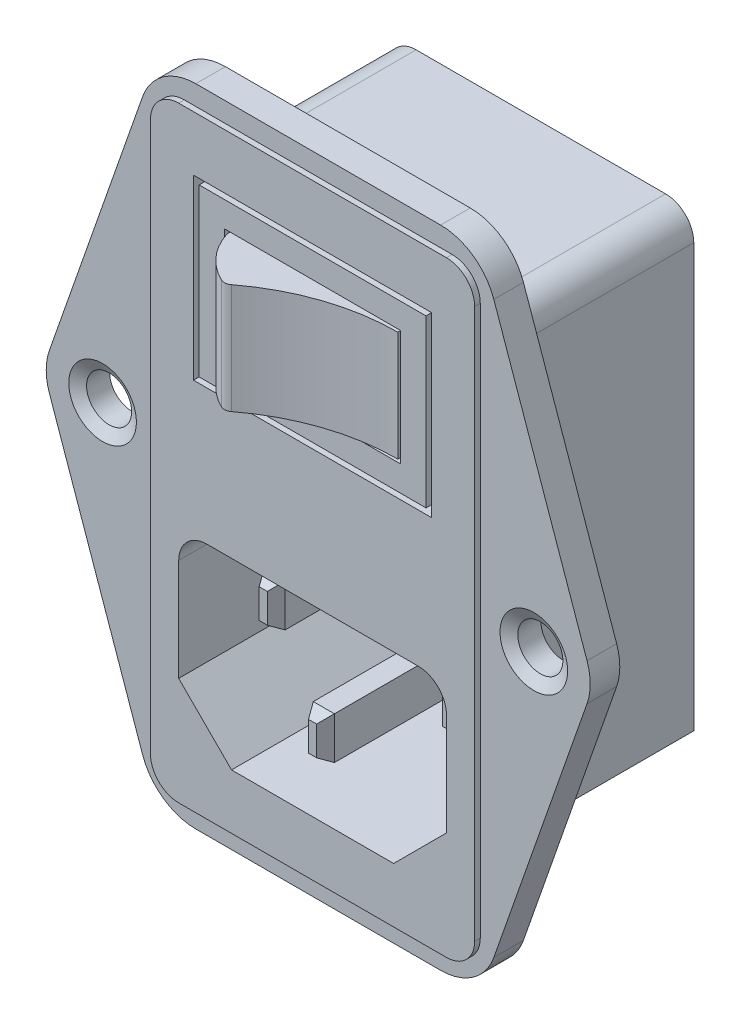
SolidWorks part; units mm, degrees
ref_plane "Front" through (0, 0, 0) normal (0, 0, 1) x (1, 0, 0)
ref_plane "Top" through (0, 0, 0) normal (0, 1, 0) x (1, 0, 0)
ref_plane "Right" through (0, 0, 0) normal (1, 0, 0) x (0, 0, -1)
sketch "Sketch1" plane through (0, 0, 0) normal (0, 0, 1) x (1, 0, 0)
  line L0 (-11.0305, 29.083) -> (11.0305, 29.083)
  line L1 (15.8253, 25.6811) -> (24.2258, 1.6781)
  line L2 (24.2258, -1.6781) -> (15.8253, -25.6811)
  line L3 (11.0305, -29.083) -> (-11.0305, -29.083)
  line L4 (-15.8253, -25.6811) -> (-24.2258, -1.6781)
  line L5 (-24.2258, 1.6781) -> (-15.8253, 25.6811)
  line L6 (-24.511, 0) -> (24.511, 0) construction
  line L7 (0, 29.083) -> (0, -29.083) construction
  line L8 (-13.97, 28.1461) -> (13.97, 28.1461) construction
  arc A0 (-11.0305, -29.083) -> (-15.8253, -25.6811) centre (-11.0305, -24.003) cw
  arc A1 (15.8253, -25.6811) -> (11.0305, -29.083) centre (11.0305, -24.003) cw
  arc A2 (24.2258, 1.6781) -> (24.2258, -1.6781) centre (19.431, 0) cw
  arc A3 (11.0305, 29.083) -> (15.8253, 25.6811) centre (11.0305, 24.003) cw
  arc A4 (-11.0305, 29.083) -> (-15.8253, 25.6811) centre (-11.0305, 24.003) ccw
  arc A5 (-24.2258, -1.6781) -> (-24.2258, 1.6781) centre (-19.431, 0) cw
  dimension "D2" = 5.08
  dimension "D1" = 58.166
  dimension "D3" = 49.022
  dimension "D4" = 27.94
extrude "Boss-Extrude1" add sketch "Sketch1" along normal blind 3.175
sketch "Sketch2" plane through (0, 0, 3.175) normal (0, 0, 1) x (1, 0, 0)
  line L0 (-14.605, 0) -> (0, 0) construction
  line L1 (-12.065, 27.305) -> (12.065, 27.305)
  line L2 (-14.605, 24.765) -> (-14.605, -24.765)
  line L3 (-12.065, -27.305) -> (12.065, -27.305)
  line L4 (14.605, 24.765) -> (14.605, -24.765)
  line L5 (0, 0) -> (0, 27.305) construction
  line L12 (-11.0305, -29.083) -> (11.0305, -29.083)
  line L13 (15.8253, -25.6811) -> (24.2258, -1.6781)
  line L14 (24.2258, 1.6781) -> (15.8253, 25.6811)
  line L15 (11.0305, 29.083) -> (-11.0305, 29.083)
  line L16 (-15.8253, 25.6811) -> (-24.2258, 1.6781)
  line L17 (-24.2258, -1.6781) -> (-15.8253, -25.6811)
  line L18 (-11.0305, -29.083) -> (11.0305, -29.083)
  line L19 (15.8253, -25.6811) -> (24.2258, -1.6781)
  line L20 (24.2258, 1.6781) -> (15.8253, 25.6811)
  line L21 (11.0305, 29.083) -> (-11.0305, 29.083)
  line L22 (-15.8253, 25.6811) -> (-24.2258, 1.6781)
  line L23 (-24.2258, -1.6781) -> (-15.8253, -25.6811)
  arc A1 (-14.605, -24.765) -> (-12.065, -27.305) centre (-12.065, -24.765) ccw
  arc A2 (12.065, -27.305) -> (14.605, -24.765) centre (12.065, -24.765) ccw
  arc A3 (12.065, 27.305) -> (14.605, 24.765) centre (12.065, 24.765) cw
  arc A4 (-12.065, 27.305) -> (-14.605, 24.765) centre (-12.065, 24.765) ccw
  arc A11 (-15.8253, -25.6811) -> (-11.0305, -29.083) centre (-11.0305, -24.003) ccw
  arc A12 (11.0305, -29.083) -> (15.8253, -25.6811) centre (11.0305, -24.003) ccw
  arc A13 (24.2258, -1.6781) -> (24.2258, 1.6781) centre (19.431, 0) ccw
  arc A14 (15.8253, 25.6811) -> (11.0305, 29.083) centre (11.0305, 24.003) ccw
  arc A15 (-11.0305, 29.083) -> (-15.8253, 25.6811) centre (-11.0305, 24.003) ccw
  arc A16 (-24.2258, 1.6781) -> (-24.2258, -1.6781) centre (-19.431, 0) ccw
  arc A17 (-15.8253, -25.6811) -> (-11.0305, -29.083) centre (-11.0305, -24.003) ccw
  arc A18 (11.0305, -29.083) -> (15.8253, -25.6811) centre (11.0305, -24.003) ccw
  arc A19 (24.2258, -1.6781) -> (24.2258, 1.6781) centre (19.431, 0) ccw
  arc A20 (15.8253, 25.6811) -> (11.0305, 29.083) centre (11.0305, 24.003) ccw
  arc A21 (-11.0305, 29.083) -> (-15.8253, 25.6811) centre (-11.0305, 24.003) ccw
  arc A22 (-24.2258, 1.6781) -> (-24.2258, -1.6781) centre (-19.431, 0) ccw
  point P12 (14.605, -27.305)
  dimension "D3" = 2.54
  dimension "D1" = 29.21
  dimension "D2" = 54.61
  dimension "D4" = 0
extrude "Cut-Extrude1" cut sketch "Sketch2" against normal blind 0.508
sketch "Sketch3" plane through (0, 0, 3.175) normal (0, 0, 1) x (1, 0, 0)
  line L0 (11.0305, 29.083) -> (-11.0305, 29.083) construction
  line L1 (-7.9375, 19.558) -> (7.9375, 19.558)
  line L2 (-7.9375, 19.558) -> (-7.9375, 9.144)
  line L3 (-7.9375, 9.144) -> (7.9375, 9.144)
  line L4 (7.9375, 19.558) -> (7.9375, 9.144)
  line L5 (0, 19.558) -> (0, 29.083) construction
  line L6 (10.2235, 21.844) -> (10.2235, 6.858)
  line L7 (-10.2235, 6.858) -> (10.2235, 6.858)
  line L8 (-10.2235, 21.844) -> (-10.2235, 6.858)
  line L9 (-10.2235, 21.844) -> (10.2235, 21.844)
  line L10 (-10.7315, 22.352) -> (10.7315, 22.352)
  line L11 (10.7315, 22.352) -> (10.7315, 6.35)
  line L12 (-10.7315, 6.35) -> (10.7315, 6.35)
  line L13 (-10.7315, 22.352) -> (-10.7315, 6.35)
  dimension "D1" = 9.525
  dimension "D2" = 10.414
  dimension "D3" = 15.875
  dimension "D4" = 2.286
  dimension "D5" = 0.508
extrude "Cut-Extrude2" cut sketch "Sketch3" against normal blind 2.54
ref_plane "Plane1" through (0, 19.304, 0) normal (0, -1, 0) x (-1, 0, 0)
sketch "Sketch5" plane through (0, 19.304, 0) normal (0, -1, 0) x (1, 0, 0)
  line L0 (-7.6835, 0.635) -> (-7.6835, 3.175)
  line L1 (-10.7315, 0.635) -> (10.7315, 0.635) construction
  line L2 (-12.065, 3.175) -> (12.065, 3.175) construction
  line L3 (7.6835, 3.175) -> (7.6835, 0.635)
  line L4 (7.6835, 0.635) -> (-7.6835, 0.635)
  line L5 (-12.065, 3.175) -> (-14.605, 3.175) construction
  arc A0 (-7.6835, 3.175) -> (-4.3138, 7.0522) centre (-1.6154, 1.3041) cw
  arc A1 (-3.5273, 6.9679) -> (7.6835, 3.175) centre (7.6835, 21.6396) ccw
  arc A2 (-4.3138, 7.0522) -> (-3.5273, 6.9679) centre (-3.99, 6.3624) cw
  point P19 (-3.8735, 7.239)
  dimension "D5" = 6.35
  dimension "D6" = 0.762
  dimension "D1" = 4.064
  dimension "D2" = 0.254
  dimension "D3" = 0.254
  dimension "D4" = 3.81
extrude "Boss-Extrude3" add sketch "Sketch5" along normal offset from surface (9.906 mm away) 0.254 up to face at (0, 9.144, 1.905)
sketch "Sketch6" plane through (0, 0, 0) normal (0, 0, -1) x (-1, 0, 0)
  line L0 (-13.7795, -19.05) -> (-7.4295, -25.4)
  line L1 (-11.2395, 21.59) -> (11.2395, 21.59)
  line L2 (-13.7795, 19.05) -> (-13.7795, -19.05)
  line L3 (-7.4295, -25.4) -> (7.4295, -25.4)
  line L4 (13.7795, 19.05) -> (13.7795, -19.05)
  line L5 (7.4295, -25.4) -> (13.7795, -19.05)
  line L6 (0, 21.59) -> (0, 0) construction
  line L7 (0, 0) -> (-13.7795, 0) construction
  arc A0 (11.2395, 21.59) -> (13.7795, 19.05) centre (11.2395, 19.05) cw
  arc A1 (-11.2395, 21.59) -> (-13.7795, 19.05) centre (-11.2395, 19.05) ccw
  point P1 (13.7795, -25.4)
  point P2 (-13.7795, -25.4)
  dimension "D3" = 2.54
  dimension "D1" = 46.99
  dimension "D2" = 27.559
extrude "Boss-Extrude4" add sketch "Sketch6" along normal blind 17.399
sketch "Sketch7" plane through (0, 0, 3.175) normal (0, 0, 1) x (1, 0, 0)
  line L0 (-7.3025, -22.352) -> (7.3025, -22.352)
  line L1 (7.3025, -22.352) -> (12.065, -17.5895)
  line L2 (12.065, -17.5895) -> (12.065, -5.842)
  line L3 (12.065, -5.842) -> (-12.065, -5.842)
  line L4 (-12.065, -5.842) -> (-12.065, -17.5895)
  line L5 (-12.065, -17.5895) -> (-7.3025, -22.352)
  line L6 (0, 0) -> (0, -22.352) construction
  line L7 (-9.2075, -10.033) -> (-7.3025, -10.033)
  line L8 (-9.2075, -10.033) -> (-9.2075, -13.843)
  line L9 (-9.2075, -13.843) -> (-7.3025, -13.843)
  line L10 (-7.3025, -10.033) -> (-7.3025, -13.843)
  line L11 (-0.9525, -14.351) -> (0.9525, -14.351)
  line L12 (-0.9525, -14.351) -> (-0.9525, -18.161)
  line L13 (-0.9525, -18.161) -> (0.9525, -18.161)
  line L14 (0.9525, -14.351) -> (0.9525, -18.161)
  line L15 (7.3025, -10.033) -> (9.2075, -10.033)
  line L16 (7.3025, -10.033) -> (7.3025, -13.843)
  line L17 (7.3025, -13.843) -> (9.2075, -13.843)
  line L18 (9.2075, -10.033) -> (9.2075, -13.843)
  line L19 (0, -14.351) -> (0, -22.352) construction
  line L20 (-11.0305, -29.083) -> (11.0305, -29.083) construction
  point P19 (-8.255, -10.033)
  dimension "D1" = 16.51
  dimension "D2" = 24.13
  dimension "D3" = 1.905
  dimension "D4" = 3.81
  dimension "D5" = 6.35
  dimension "D6" = 6.35
  dimension "D7" = 0.508
  dimension "D8" = 4.191
  dimension "D9" = 135
  dimension "D10" = 4.7625
  dimension "D11" = 6.731
extrude "Cut-Extrude3" cut sketch "Sketch7" against normal blind 16.51
sketch "Sketch8" plane through (0, 0, 3.175) normal (0, 0, 1) x (1, 0, 0)
  line L4 (7.3025, -10.033) -> (7.3025, -13.843)
  line L5 (7.3025, -13.843) -> (9.2075, -13.843)
  line L6 (9.2075, -13.843) -> (9.2075, -10.033)
  line L7 (9.2075, -10.033) -> (7.3025, -10.033)
  line L8 (7.3025, -10.033) -> (7.3025, -13.843)
  line L9 (7.3025, -13.843) -> (9.2075, -13.843)
  line L10 (9.2075, -13.843) -> (9.2075, -10.033)
  line L11 (9.2075, -10.033) -> (7.3025, -10.033)
  line L12 (-9.2075, -10.033) -> (-9.2075, -13.843)
  line L13 (-9.2075, -13.843) -> (-7.3025, -13.843)
  line L14 (-7.3025, -13.843) -> (-7.3025, -10.033)
  line L15 (-7.3025, -10.033) -> (-9.2075, -10.033)
  line L16 (-9.2075, -10.033) -> (-9.2075, -13.843)
  line L17 (-9.2075, -13.843) -> (-7.3025, -13.843)
  line L18 (-7.3025, -13.843) -> (-7.3025, -10.033)
  line L19 (-7.3025, -10.033) -> (-9.2075, -10.033)
  dimension "D1" = 0
  dimension "D2" = 0
extrude "Cut-Extrude4" cut sketch "Sketch8" against normal blind 3.81
chamfer "Chamfer1" distance 1.016 angle 30 12 edges at (0, -14.351, 3.175) (0.9525, -16.256, 3.175) (0, -18.161, 3.175) (-0.9525, -16.256, 3.175) (9.2075, -11.938, -0.635) (8.255, -13.843, -0.635) (7.3025, -11.938, -0.635) (8.255, -10.033, -0.635) (-7.3025, -11.938, -0.635) (-8.255, -13.843, -0.635) (-9.2075, -11.938, -0.635) (-8.255, -10.033, -0.635)
fillet "Fillet1" radius 2.54 2 edges at (-12.065, -5.842, -5.08) (12.065, -5.842, -5.08)
sketch "Sketch9" plane through (0, 0, 2.667) normal (0, 0, 1) x (1, 0, 0)
  circle A0 centre (-19.431, 0) radius 2.032
  circle A1 centre (19.431, 0) radius 2.032
  arc A3 (-24.2258, 1.6781) -> (-24.2258, -1.6781) centre (-19.431, 0) ccw construction
  arc A5 (24.2258, -1.6781) -> (24.2258, 1.6781) centre (19.431, 0) ccw construction
  dimension "D1" = 4.064
extrude "Cut-Extrude5" cut sketch "Sketch9" against normal through all
chamfer "Chamfer2" distance 1.016 angle 30 2 edges at (21.463, 0, 2.667) (-17.399, 0, 2.667)
